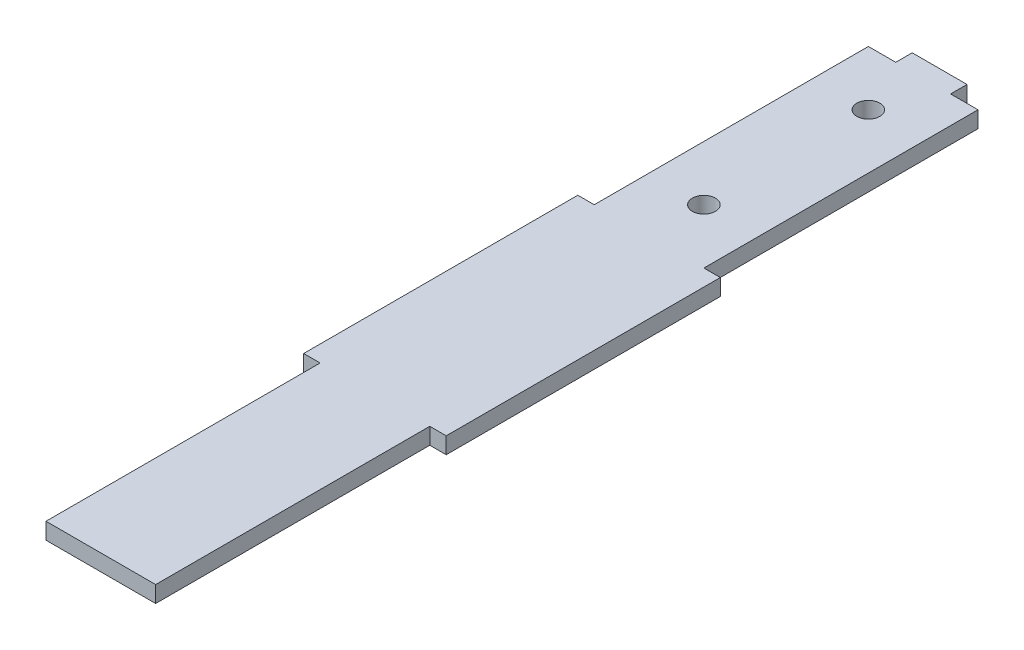
SolidWorks part; units mm, degrees
ref_plane "Front Plane" through (0, 0, 0) normal (0, 0, 1) x (1, 0, 0)
ref_plane "Top Plane" through (0, 0, 0) normal (0, 1, 0) x (1, 0, 0)
ref_plane "Right Plane" through (0, 0, 0) normal (1, 0, 0) x (0, 0, -1)
sketch "Sketch1" plane through (0, 0, 0) normal (0, 1, 0) x (1, 0, 0)
  line L0 (15, 0) -> (20, 0)
  line L1 (0, 0) -> (5, 0)
  line L2 (0, 0) -> (0, -50)
  line L3 (0, -150) -> (20, -150)
  line L4 (20, 0) -> (20, -50)
  line L5 (0, -50) -> (-3, -50)
  line L7 (0, -100) -> (-3, -100)
  line L8 (-3, -50) -> (-3, -100)
  line L9 (20, -50) -> (23, -50)
  line L11 (20, -100) -> (23, -100)
  line L12 (23, -50) -> (23, -100)
  line L13 (5, 3) -> (15, 3)
  line L14 (5, 3) -> (5, 0)
  line L16 (15, 3) -> (15, 0)
  line L17 (0, -100) -> (0, -150)
  line L18 (20, -100) -> (20, -150)
  point P17 (-3, -75)
  point P19 (10, 3)
  dimension "D1" = 20
  dimension "D2" = 150
  dimension "D3" = 3
  dimension "D4" = 10
  dimension "D5" = 50
extrude "Boss-Extrude1" add sketch "Sketch1" along normal blind 3
sketch "Sketch2" plane through (0, 3, 0) normal (0, 1, 0) x (1, 0, 0)
  line L0 (10, 3) -> (10, -150) construction
  line L1 (15, 3) -> (5, 3) construction
  line L2 (0, -150) -> (20, -150) construction
  line L3 (20, 0) -> (15, 0) construction
  circle A0 centre (10, -10) radius 2.1
  circle A1 centre (10, -40) radius 2.1
  dimension "D1" = 4.2
  dimension "D2" = 10
  dimension "D3" = 30
extrude "Cut-Extrude1" cut sketch "Sketch2" against normal through all
